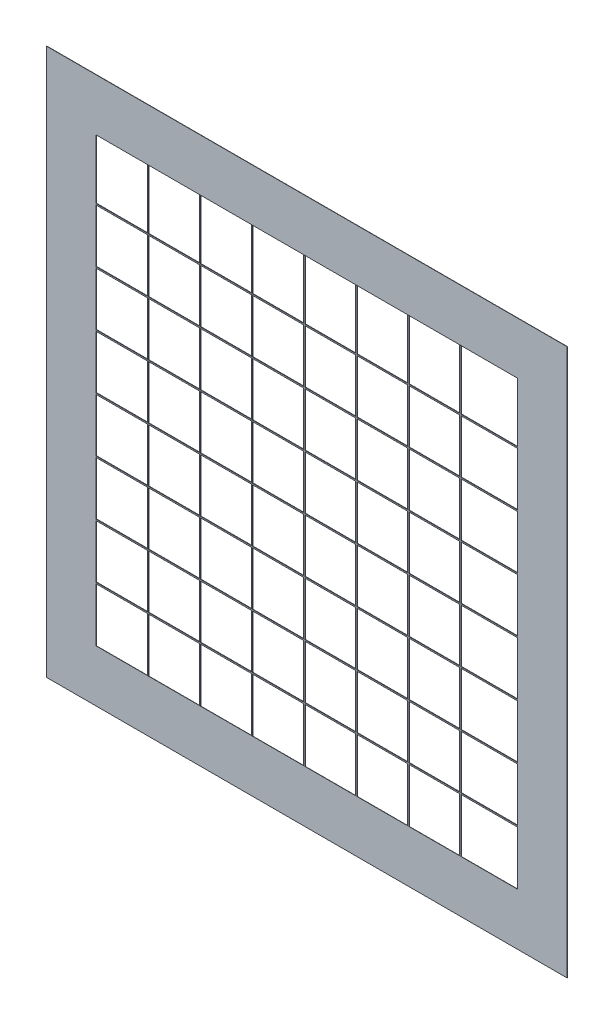
SolidWorks part; units mm, degrees
ref_plane "前视基准面" through (0, 0, 0) normal (0, 0, 1) x (1, 0, 0)
ref_plane "上视基准面" through (0, 0, 0) normal (0, 1, 0) x (1, 0, 0)
ref_plane "右视基准面" through (0, 0, 0) normal (1, 0, 0) x (0, 0, -1)
sketch "草图2" plane through (0, 0, 0) normal (0, 0, 1) x (1, 0, 0)
  line L1 (205, -31.8937) -> (5, -31.8937)
  line L2 (205, -31.8937) -> (205, -241.8937)
  line L3 (205, -241.8937) -> (5, -241.8937)
  line L4 (5, -31.8937) -> (5, -241.8937)
  line L5 (205, -31.8937) -> (5, -241.8937) construction
  line L6 (205, -241.8937) -> (5, -31.8937) construction
  line L7 (105, -241.15) -> (105, -101.7594) construction
  line L9 (205.5, -241.15) -> (4.5, -241.15) construction
  line L11 (24.0476, -221.8937) -> (185.9524, -221.8937)
  line L12 (24.0476, -221.8937) -> (24.0476, -51.8937)
  line L13 (24.0476, -51.8937) -> (185.9524, -51.8937)
  line L14 (185.9524, -221.8937) -> (185.9524, -51.8937)
  line L15 (24.0476, -221.8937) -> (185.9524, -51.8937) construction
  line L16 (24.0476, -51.8937) -> (185.9524, -221.8937) construction
  point P0 (105, -136.8937)
  point P9 (105, -136.8937)
  dimension "D1" = 210
  dimension "D2" = 200
  dimension "D3" = 20
extrude "凸台-拉伸1" add sketch "草图2" along normal blind 0.1
sketch "草图3" plane through (0, 0, 0) normal (0, 0, 1) x (1, 0, 0)
  line L1 (44.0476, -51.8937) -> (44.0476, -221.8937)
  line L2 (64.0476, -51.8937) -> (64.0476, -221.8937)
  line L3 (84.0476, -51.8937) -> (84.0476, -221.8937)
  line L4 (104.0476, -51.8937) -> (104.0476, -221.8937)
  line L5 (124.0476, -51.8937) -> (124.0476, -221.8937)
  line L6 (144.0476, -51.8937) -> (144.0476, -221.8937)
  line L7 (164.0476, -51.8937) -> (164.0476, -221.8937)
  line L8 (24.0476, -200.8937) -> (185.9524, -200.8937)
  line L9 (24.0476, -179.8937) -> (185.9524, -179.8937)
  line L10 (24.0476, -158.8937) -> (185.9524, -158.8937)
  line L11 (24.0476, -137.8937) -> (185.9524, -137.8937)
  line L12 (24.0476, -116.8937) -> (185.9524, -116.8937)
  line L13 (24.0476, -95.8937) -> (185.9524, -95.8937)
  line L14 (24.0476, -74.8937) -> (185.9524, -74.8937)
extrude "拉伸-薄壁1" add sketch "草图3" along normal blind 0.2 separate body thin thin type mid plane wall 0.5
